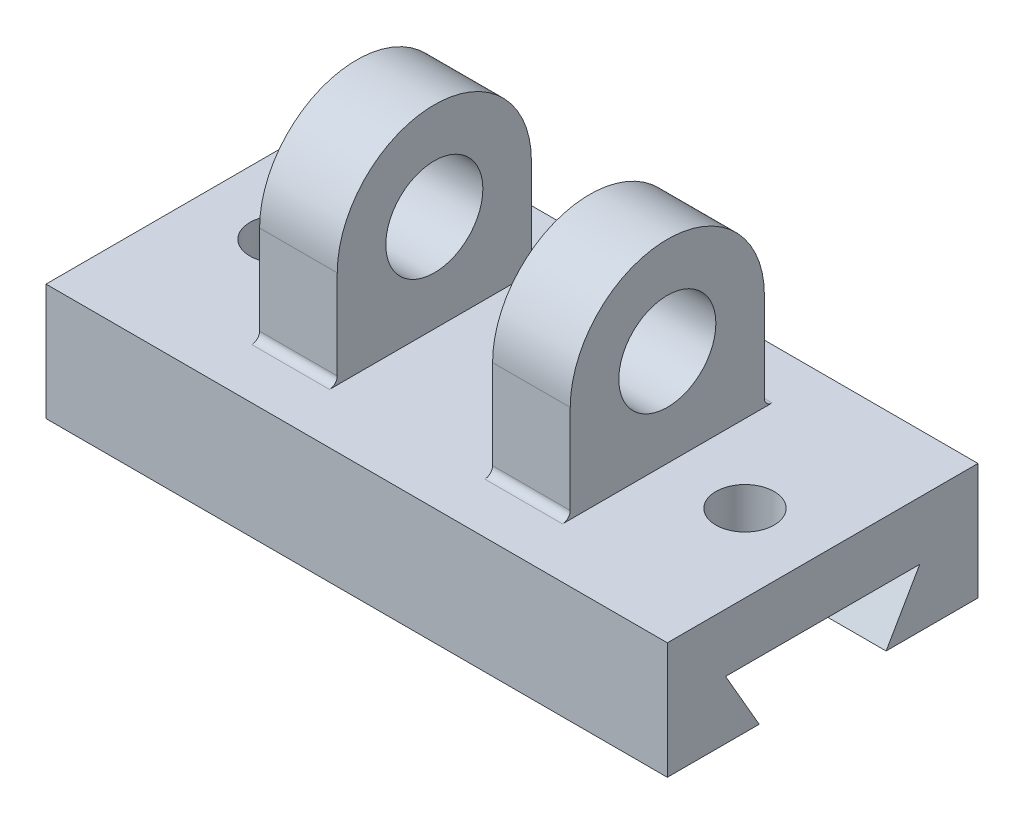
SolidWorks part; units mm, degrees
ref_plane "Front Plane" through (0, 0, 0) normal (0, 0, 1) x (1, 0, 0)
ref_plane "Top Plane" through (0, 0, 0) normal (0, 1, 0) x (1, 0, 0)
ref_plane "Right Plane" through (0, 0, 0) normal (1, 0, 0) x (0, 0, -1)
sketch "Sketch2" plane through (0, 0, 0) normal (0, 1, 0) x (1, 0, 0)
  line L0 (0, -55) -> (0, 55) construction
  line L1 (-80, 40) -> (80, 40)
  line L2 (-80, 40) -> (-80, -40)
  line L3 (-80, -40) -> (80, -40)
  line L4 (80, 40) -> (80, -40)
  line L5 (-80, 40) -> (80, -40) construction
  line L6 (-80, -40) -> (80, 40) construction
  point P1 (0, 0)
  dimension "D1" = 160
  dimension "D2" = 80
extrude "Boss-Extrude1" add sketch "Sketch2" along normal blind 30
sketch "Sketch3" plane through (80, 0, 0) normal (1, 0, 0) x (0, 0, -1)
  line L0 (-40, 0) -> (-16.3397, 0)
  line L1 (-40, 0) -> (40, 0) construction
  line L2 (-16.3397, 0) -> (-25, 15)
  line L3 (-25, 15) -> (25, 15)
  line L4 (25, 15) -> (16.3397, 0)
  line L5 (16.3397, 0) -> (-16.3397, 0)
  line L6 (-40, 30) -> (40, 30) construction
  line L7 (40, 30) -> (40, 0) construction
  line L8 (-40, 30) -> (-40, 0) construction
  line M10 (-40, 0) -> (40, 0)
  dimension "D1" = 15
  dimension "D2" = 15
  dimension "D3" = 15
  dimension "D4" = 60
  dimension "D5" = 60
extrude "Cut-Extrude1" cut sketch "Sketch3" against normal through all contours L4 L3 L2 M10
sketch "Sketch4" plane through (0, 30, 0) normal (0, 1, 0) x (1, 0, 0)
  line L0 (80, -40) -> (80, 40) construction
  line L2 (-80, -40) -> (80, -40) construction
  circle A0 centre (60, 0) radius 7.5
  point P6 (61.2903, -40)
  point P7 (80, -3.5182)
  dimension "D1" = 15
  dimension "D2" = 20
  dimension "D3" = 40
extrude "Cut-Extrude2" cut sketch "Sketch4" against normal through all
sketch "Sketch5" plane through (80, 0, 0) normal (1, 0, 0) x (0, 0, -1)
  line L0 (-40, 30) -> (40, 30) construction
  line L2 (-25, 55) -> (25, 55)
  line L3 (-25, 55) -> (-25, 30)
  line L5 (25, 55) -> (25, 30)
  circle A1 centre (0, 55) radius 12.5
  arc A2 (25, 55) -> (-25, 55) centre (0, 55) ccw
  point P4 (0, 30)
  line M9 (40, 30) -> (-40, 30)
  dimension "D2" = 25
  dimension "D3" = 25
  dimension "D1" = 50
extrude "Boss-Extrude2" add sketch "Sketch5" against normal blind 20 from offset 40 contours A1 L2 L3 L5 M9 | L2 A2 A1 offset against normal yes
ref_plane "Plane1" through (0, 0, 0) normal (1, 0, 0) x (0, 0, -1)
mirror "Mirror1" about plane through (0, 0, 0) normal (1, 0, 0) of "Cut-Extrude2", "Boss-Extrude2"
fillet "Fillet1" radius 2 4 edges at (-30, 30, -25) (30, 30, -25) (30, 30, 25) (-30, 30, 25)
